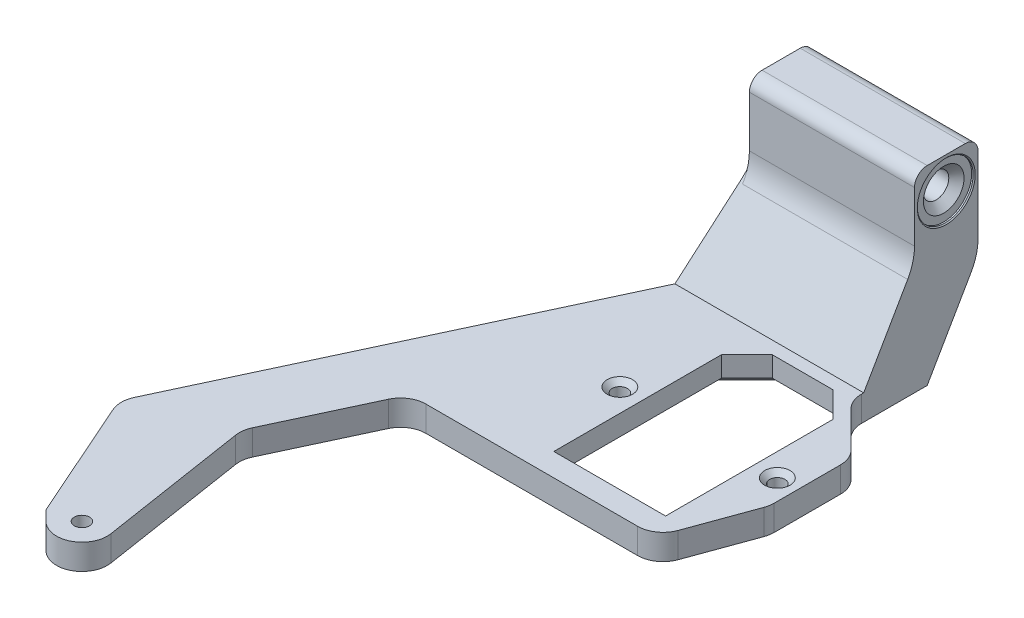
SolidWorks part; units mm, degrees
ref_plane "Front" through (0, 0, 0) normal (0, 0, 1) x (1, 0, 0)
ref_plane "Top" through (0, 0, 0) normal (0, 1, 0) x (1, 0, 0)
ref_plane "Right" through (0, 0, 0) normal (1, 0, 0) x (0, 0, -1)
sketch "Sketch1" plane through (0, 0, 0) normal (0, 1, 0) x (1, 0, 0)
  line L1 (-35.6381, -156.0824) -> (-28.5941, -163.1265)
  line L2 (-28.5941, -163.1265) -> (-21.8229, -156.3553)
  line L3 (41.275, -31.75) -> (41.275, 0)
  line L5 (0, 0) -> (41.275, 0)
  line L6 (41.275, -15.875) -> (0, -15.875) construction
  line L7 (-28.5941, -163.1265) -> (-28.5941, -154.1463) construction
  line L9 (-21.8229, -156.3553) -> (-28.3802, -114.3)
  line L11 (0, 0) -> (0, -15.875)
  line L13 (0, -7.9375) -> (41.275, -7.9375) construction
  line L14 (-28.3802, -114.3) -> (-15.0555, -85.725)
  line L15 (-15.0555, -85.725) -> (46.355, -85.725)
  line L17 (0, -15.875) -> (-50.1169, -123.351)
  line L18 (-50.1169, -123.351) -> (-35.6381, -156.0824)
  line L20 (53.975, -64.7892) -> (53.975, -44.45)
  line L21 (53.975, -44.45) -> (41.275, -31.75)
  line L22 (46.355, -85.725) -> (53.975, -64.7892)
  circle A0 centre (-28.5941, -154.1463) radius 1.905
  circle A1 centre (-28.5941, -154.1463) radius 6.35
  point P11 (53.975, -85.725)
  dimension "D1" = 28.5941
  dimension "D5" = 12.7
  dimension "D7" = 3.81
  dimension "D2" = 15.875
  dimension "D3" = 154.1463
  dimension "D4" = 115
  dimension "D6" = 15.875
  dimension "D8" = 15
  dimension "D9" = 114.3
  dimension "D10" = 85.725
  dimension "D11" = 53.975
  dimension "D12" = 41.275
  dimension "D13" = 45
  dimension "D14" = 7.62
  dimension "D15" = 70
extrude "Boss-Extrude1" add sketch "Sketch1" along normal blind 6.35
sketch "Sketch2" plane through (0, 6.35, 0) normal (0, 1, 0) x (1, 0, 0)
  line L0 (41.275, -31.75) -> (41.275, 0) construction
  line L1 (0, 0) -> (41.275, 0)
  line L2 (0, 0) -> (0, -15.875)
  line L3 (0, -15.875) -> (41.275, -15.875)
  line L4 (41.275, 0) -> (41.275, -15.875)
extrude "Boss-Extrude2" add sketch "Sketch2" along normal blind 41.275 contours L3 L4 L1 L2
sketch "Sketch3" plane through (41.275, 0, 0) normal (1, 0, 0) x (0, 0, -1)
  line L0 (-7.9375, 47.625) -> (-7.9375, 39.6875) construction
  line L1 (0, 47.625) -> (-15.875, 47.625) construction
  circle A0 centre (-7.9375, 39.6875) radius 3.175
  dimension "D1" = 6.35
  dimension "D2" = 7.9375
extrude "Cut-Extrude1" cut sketch "Sketch3" against normal through all
sketch "Sketch4" plane through (41.275, 0, 0) normal (1, 0, 0) x (0, 0, -1)
  circle A0 centre (-7.9375, 39.6875) radius 6.985
  dimension "D1" = 13.97
extrude "Cut-Extrude2" cut sketch "Sketch4" against normal blind 0.635
ref_plane "Plane1" through (20.6375, 0, 0) normal (1, 0, 0) x (0, 0, -1)
mirror "Mirror1" about plane through (20.6375, 0, 0) normal (1, 0, 0) of "Cut-Extrude2"
chamfer "Chamfer1" distance 0.254 angle 45 2 edges at (0, 39.6875, 0.9525) (41.275, 39.6875, 0.9525)
chamfer "Chamfer2" distance 1.905 angle 45 2 edges at (0.635, 39.6875, 11.1125) (40.64, 39.6875, 4.7625)
fillet "Fillet3" radius 3.175 2 edges at (20.6375, 47.625, 0) (20.6375, 47.625, 15.875)
chamfer "Chamfer3" distance 12.7 angle 60 1 edges at (20.6375, 6.35, 15.875)
sketch "Sketch6" plane through (0, 6.35, 0) normal (0, 1, 0) x (1, 0, 0)
  line L0 (29.21, -57.785) -> (9.525, -57.785) construction
  line L1 (21.59, -31.75) -> (36.83, -31.75)
  line L2 (15.24, -38.1) -> (15.24, -80.01)
  line L3 (15.24, -80.01) -> (43.18, -80.01)
  line L4 (43.18, -38.1) -> (43.18, -80.01)
  line L5 (29.21, -57.785) -> (48.895, -57.785) construction
  line L6 (15.24, -38.1) -> (21.59, -31.75)
  line L7 (36.83, -31.75) -> (43.18, -38.1)
  line L9 (0, 0) -> (0, -15.875) construction
  line L23 (29.21, -31.75) -> (29.21, -80.01) construction
  line L24 (29.21, -57.785) -> (26.8307, -57.785) construction
  line L25 (26.8307, -57.785) -> (29.21, -57.785) construction
  circle A0 centre (9.525, -57.785) radius 1.905
  circle A1 centre (48.895, -57.785) radius 1.905
  point P0 (15.24, -31.75)
  point P3 (43.18, -31.75)
  dimension "D4" = 3.81
  dimension "D5" = 29.21
  dimension "D1" = 27.94
  dimension "D2" = 48.26
  dimension "D3" = 39.37
  dimension "D6" = 31.75
  dimension "D9" = 26.035
extrude "Cut-Extrude3" cut sketch "Sketch6" against normal blind 6.35
fillet "Fillet4" radius 6.35 8 edges at (0, 14.1735, 15.875) (-28.3802, 3.175, 114.3) (-15.0555, 3.175, 85.725) (-50.1169, 3.175, 123.351) (53.975, 3.175, 44.45) (41.275, 3.175, 31.75) (53.975, 3.175, 64.7892) (46.355, 3.175, 85.725)
chamfer "Chamfer4" distance 1.27 angle 45 2 edges at (9.525, 6.35, 59.69) (48.895, 6.35, 59.69)
chamfer "Chamfer5" distance 12.7 angle 60 1 edges at (20.6375, 0, 0)
fillet "Fillet5" radius 12.7 2 edges at (20.6375, 21.997, 0) (20.6375, 28.347, 15.875)
chamfer "Chamfer6" distance 1.27 angle 45 6 edges at (40.005, 0, 34.925) (43.18, 0, 59.055) (29.21, 0, 80.01) (29.21, 0, 31.75) (15.24, 0, 59.055) (18.415, 0, 34.925)
sketch "Sketch7" plane through (0, 5.4993, 9.525) normal (0, -0.5, -0.866) x (-1, 0, 0)
  line L0 (-41.275, 6.35) -> (0, 6.35) construction
  line L1 (-41.275, -6.35) -> (-41.275, 15.647) construction
  line L2 (0, -6.35) -> (-41.275, -6.35) construction
  line L3 (0, 15.647) -> (0, -6.35) construction
  text T0 "<b>LCSKEL-1</b>"
  dimension "D1" = 12.7
extrude "Cut-Extrude4" cut sketch "Sketch7" against normal blind 1.27
